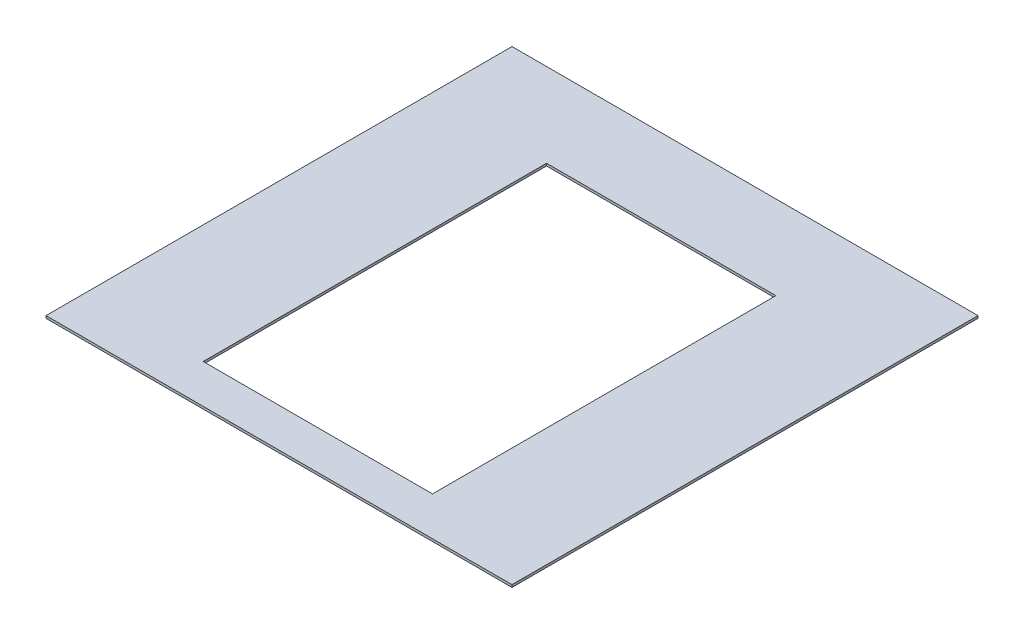
SolidWorks part; units mm, degrees
ref_plane "Front Plane" through (0, 0, 0) normal (0, 0, 1) x (1, 0, 0)
ref_plane "Top Plane" through (0, 0, 0) normal (0, 1, 0) x (1, 0, 0)
ref_plane "Right Plane" through (0, 0, 0) normal (1, 0, 0) x (0, 0, -1)
sketch "Sketch1" plane through (0, 0, 0) normal (0, 1, 0) x (1, 0, 0)
  line L0 (0, 0) -> (0, 195.2) construction
  line L1 (-304.8, -304.8) -> (304.8, -304.8)
  line L2 (-304.8, -304.8) -> (-304.8, 304.8)
  line L3 (-304.8, 304.8) -> (304.8, 304.8)
  line L4 (304.8, -304.8) -> (304.8, 304.8)
  line L5 (-304.8, -304.8) -> (304.8, 304.8) construction
  line L6 (-304.8, 304.8) -> (304.8, -304.8) construction
  line L7 (-150, 195.2) -> (150, 195.2)
  line L8 (-150, 195.2) -> (-150, -254)
  line L9 (-150, -254) -> (150, -254)
  line L10 (150, 195.2) -> (150, -254)
  point P0 (0, 0)
  dimension "D1" = 609.6
  dimension "D2" = 300
  dimension "D3" = 449.2
  dimension "D4" = 50.8
extrude "Boss-Extrude1" add sketch "Sketch1" along normal mid plane 3.175
